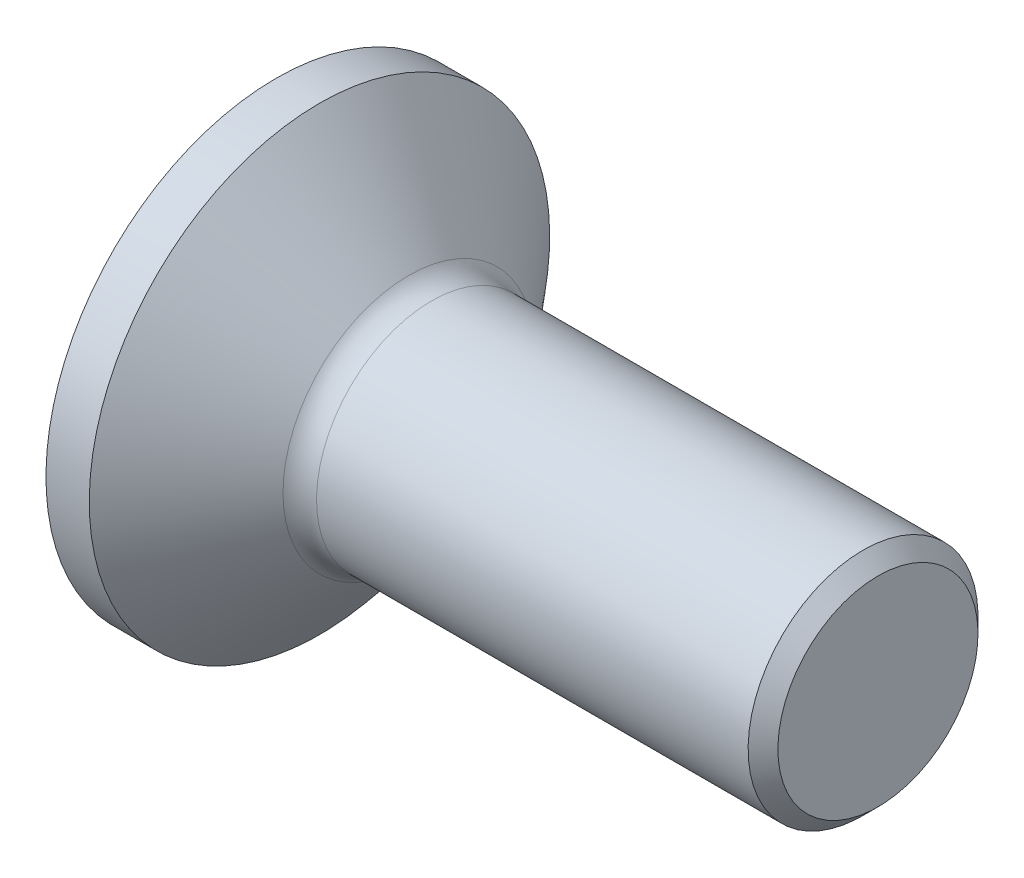
SolidWorks part; units mm, degrees
ref_plane "Front" through (0, 0, 0) normal (0, 0, 1) x (1, 0, 0)
ref_plane "Top" through (0, 0, 0) normal (0, 1, 0) x (1, 0, 0)
ref_plane "Right" through (0, 0, 0) normal (1, 0, 0) x (0, 0, -1)
sketch "Sketch1" plane through (0, 0, 0) normal (0, 0, 1) x (1, 0, 0)
  line L0 (2.5808, 1.91) -> (9.7525, 1.91)
  line L1 (9.7525, 1.91) -> (10, 1.6625)
  line L2 (10, 1.6625) -> (10, 0)
  line L3 (2.2, 2.0859) -> (0.72, 3.825)
  line L4 (0.72, 3.825) -> (0, 3.825)
  line L5 (0, 3.825) -> (0, 0)
  line L6 (0, 0) -> (10, 0)
  line L7 (0, 0) -> (-0.9177, 0) construction
  arc A0 (2.5808, 1.91) -> (2.2, 2.0859) centre (2.5808, 2.41) cw
  dimension "D1" = 10
  dimension "D4" = 0.5
  dimension "D2" = 7.65
  dimension "D3" = 0.72
  dimension "D5" = 3.82
  dimension "D6" = 135
  dimension "D7" = 0.35
  dimension "D8" = 2.2
revolve "Revolve1" add sketch "Sketch1" angle 360 about L7
sketch "Sketch2" plane through (0, 0, 0) normal (-1, 0, 0) x (0, 0, 1)
  line L1 (1.25, 0.7217) -> (0, 1.4434)
  line L2 (0, 1.4434) -> (-1.25, 0.7217)
  line L3 (-1.25, 0.7217) -> (-1.25, -0.7217)
  line L4 (-1.25, -0.7217) -> (0, -1.4434)
  line L5 (0, -1.4434) -> (1.25, -0.7217)
  line L6 (1.25, -0.7217) -> (1.25, 0.7217)
  circle A0 centre (0, 0) radius 1.25 construction
  dimension "D1" = 2.5
extrude "Cut-Extrude1" cut sketch "Sketch2" against normal blind 1.5
